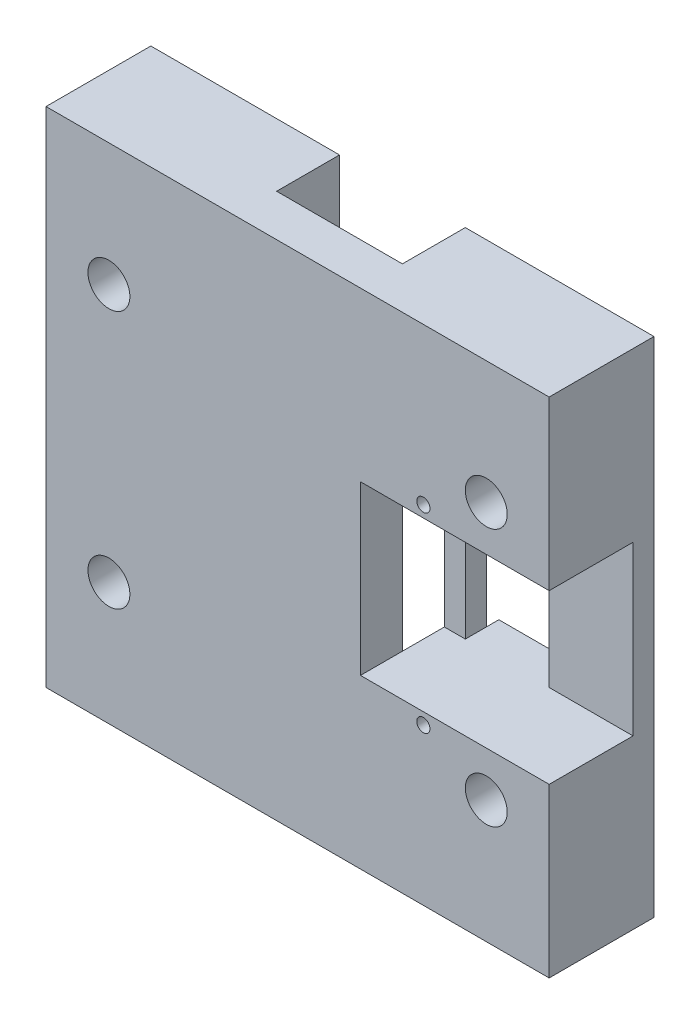
SolidWorks part; units mm, degrees
ref_plane "Front" through (0, 0, 0) normal (0, 0, 1) x (1, 0, 0)
ref_plane "Top" through (0, 0, 0) normal (0, 1, 0) x (1, 0, 0)
ref_plane "Right" through (0, 0, 0) normal (1, 0, 0) x (0, 0, -1)
sketch "Sketch1" plane through (0, 0, 0) normal (0, 0, 1) x (1, 0, 0)
  line L1 (38.1, 10) -> (-38.1, 10) construction
  line L2 (38.1, 10) -> (38.1, -10) construction
  line L3 (38.1, -10) -> (-38.1, -10) construction
  line L4 (-38.1, 10) -> (-38.1, -10) construction
  line L5 (38.1, 10) -> (-38.1, -10) construction
  line L6 (38.1, -10) -> (-38.1, 10) construction
  line L7 (38.1, 38.1) -> (-38.1, 38.1)
  line L8 (38.1, 38.1) -> (38.1, -38.1)
  line L9 (38.1, -38.1) -> (-38.1, -38.1)
  line L10 (-38.1, 38.1) -> (-38.1, -38.1)
  line L11 (38.1, 38.1) -> (-38.1, -38.1) construction
  line L12 (38.1, -38.1) -> (-38.1, 38.1) construction
  circle A0 centre (-28.575, 19.525) radius 3.175
  circle A1 centre (28.575, 19.525) radius 3.175
  circle A2 centre (28.575, -19.525) radius 3.175
  circle A3 centre (-28.575, -19.525) radius 3.175
  point P0 (0, 0)
  point P6 (0, 0)
  point P19 (0, 0)
  point P20 (0, 0)
  point P21 (0, 0)
  point P22 (0, 0)
  point P23 (0, 0)
  point P24 (0, 0)
  point P25 (-28.0713, 19.525)
  point P26 (0, 0)
  point P27 (0, 0)
  point P28 (0, 0)
  point P29 (0, 0)
  point P30 (0, 0)
  point P31 (0, 0)
  point P32 (0, 0)
  point P33 (0, 0)
  point P34 (27.3095, 19.525)
  dimension "D4" = 6.35
  dimension "D1" = 20
  dimension "D2" = 76.2
  dimension "D3" = 76.2
  dimension "D5" = 9.525
  dimension "D6" = 9.525
  dimension "D7" = 9.525
  dimension "D8" = 9.525
extrude "Boss-Extrude1" add sketch "Sketch1" along normal blind 6.35
sketch "Sketch2" plane through (0, 0, 0) normal (0, 0, -1) x (-1, 0, 0)
  line L0 (38.1, -38.1) -> (-38.1, -38.1) construction
  line L1 (9.525, 38.1) -> (-9.525, 38.1)
  line L2 (9.525, 38.1) -> (9.525, -38.1)
  line L3 (9.525, -38.1) -> (-9.525, -38.1)
  line L4 (-9.525, 38.1) -> (-9.525, -38.1)
  line L5 (9.525, 38.1) -> (-9.525, -38.1) construction
  line L6 (9.525, -38.1) -> (-9.525, 38.1) construction
  line L11 (38.1, -38.1) -> (38.1, 38.1)
  line L12 (38.1, 38.1) -> (-38.1, 38.1)
  line L13 (-38.1, 38.1) -> (-38.1, -38.1)
  line L14 (-38.1, -38.1) -> (38.1, -38.1)
  line L15 (38.1, -38.1) -> (38.1, 38.1)
  line L16 (38.1, 38.1) -> (-38.1, 38.1)
  line L17 (-38.1, 38.1) -> (-38.1, -38.1)
  line L18 (-38.1, -38.1) -> (38.1, -38.1)
  point P0 (0, 0)
  circle M6 centre (-28.575, -19.525) radius 3.175
  circle M7 centre (28.575, 19.525) radius 3.175
  line M8 (38.1, -38.1) -> (38.1, 38.1)
  line M9 (38.1, 38.1) -> (-38.1, 38.1)
  line M10 (-38.1, 38.1) -> (-38.1, -38.1)
  line M11 (-38.1, -38.1) -> (38.1, -38.1)
  circle M12 centre (-28.575, 19.525) radius 3.175
  circle M13 centre (28.575, -19.525) radius 3.175
  dimension "D1" = 19.05
  dimension "D2" = 0
extrude "Boss-Extrude3" add sketch "Sketch2" along normal blind 9.525 contours L4 M9 M10 M11 M12 M6 | L2 M9 M11 M8 M13 M7
sketch "Sketch4" plane through (9.525, 0, 0) normal (-1, 0, 0) x (0, 0, 1)
  line L1 (6.35, 12.7) -> (-6.35, 12.7)
  line L2 (6.35, 12.7) -> (6.35, -12.7)
  line L3 (6.35, -12.7) -> (-6.35, -12.7)
  line L4 (-6.35, 12.7) -> (-6.35, -12.7)
  line L5 (6.35, 12.7) -> (-6.35, -12.7) construction
  line L6 (6.35, -12.7) -> (-6.35, 12.7) construction
  line L7 (-9.525, 38.1) -> (-9.525, -38.1) construction
  point P0 (0, 0)
  point P6 (0, 0)
  point P8 (0, 0)
  dimension "D1" = 25.4
  dimension "D2" = 3.175
extrude "Cut-Extrude1" cut sketch "Sketch4" against normal up to surface (28.575 mm away) up to face at (38.1, 0, -1.5875)
sketch "Sketch5" plane through (0, 0, -9.525) normal (0, 0, -1) x (-1, 0, 0)
  line L0 (-28.575, 19.525) -> (-28.575, -19.525) construction
  line L1 (-12.7, 16.2) -> (-25.4, 16.2)
  line L2 (-12.7, 16.2) -> (-12.7, -16.2)
  line L3 (-12.7, -16.2) -> (-25.4, -16.2)
  line L4 (-25.4, 16.2) -> (-25.4, -16.2)
  line L5 (-12.7, 16.2) -> (-25.4, -16.2) construction
  line L6 (-12.7, -16.2) -> (-25.4, 16.2) construction
  line L7 (-9.525, 12.7) -> (-9.525, -12.7) construction
  line L8 (-25.4, 11.2) -> (-25.4, 16.2) construction
  line L9 (-25.4, 16.2) -> (-19.6, 16.2) construction
  point P0 (-19.05, 0)
  point P5 (-30.7455, 0)
  point P6 (0, 0)
  point P7 (0, 0)
  point P13 (-16.1648, 0)
  dimension "D3" = 3.175
extrude "Cut-Extrude2" cut sketch "Sketch5" against normal blind 9.525
sketch "Sketch6" plane through (0, 0, 0) normal (0, 0, -1) x (-1, 0, 0)
  line L0 (-25.4, 16.2) -> (-12.7, 12.7) construction
  line L1 (-25.4, -12.7) -> (-12.7, -16.2) construction
  line L4 (-12.7, 12.7) -> (-12.7, 16.2)
  line L5 (-12.7, 16.2) -> (-25.4, 16.2)
  line L6 (-25.4, 16.2) -> (-25.4, 12.7)
  line L7 (-25.4, 12.7) -> (-12.7, 12.7)
  line L8 (-12.7, 12.7) -> (-12.7, 16.2)
  line L9 (-12.7, 16.2) -> (-25.4, 16.2)
  line L10 (-25.4, 16.2) -> (-25.4, 12.7)
  line L11 (-25.4, 12.7) -> (-12.7, 12.7)
  line L12 (-25.4, -12.7) -> (-25.4, -16.2)
  line L13 (-25.4, -16.2) -> (-12.7, -16.2)
  line L14 (-12.7, -16.2) -> (-12.7, -12.7)
  line L15 (-12.7, -12.7) -> (-25.4, -12.7)
  line L16 (-25.4, -12.7) -> (-25.4, -16.2)
  line L17 (-25.4, -16.2) -> (-12.7, -16.2)
  line L18 (-12.7, -16.2) -> (-12.7, -12.7)
  line L19 (-12.7, -12.7) -> (-25.4, -12.7)
  circle A0 centre (-19.05, 14.45) radius 1
  circle A1 centre (-19.05, -14.45) radius 1
  dimension "D3" = 2
  dimension "D1" = 0
  dimension "D2" = 0
extrude "Cut-Extrude3" cut sketch "Sketch6" against normal up to surface (6.35 mm away) contours A0 | A1 up to face at (11.9063, 0, 6.35)
sketch "Sketch7" plane through (0, 0, 0) normal (0, 0, -1) x (-1, 0, 0)
  line L0 (-25.4, -12.7) -> (-25.4, -16.2) construction
  line L1 (-25.4, -16.2) -> (-12.7, -16.2) construction
  line L2 (-12.7, -16.2) -> (-12.7, -12.7) construction
  line L3 (-12.7, -12.7) -> (-25.4, -12.7) construction
  line L4 (-12.7, 12.7) -> (-12.7, 16.2) construction
  line L5 (-12.7, 16.2) -> (-25.4, 16.2) construction
  line L6 (-25.4, 16.2) -> (-25.4, 12.7) construction
  line L7 (-25.4, 12.7) -> (-12.7, 12.7) construction
  line L8 (-25.4, -12.7) -> (-25.4, -16.2)
  line L9 (-25.4, -16.2) -> (-12.7, -16.2)
  line L10 (-12.7, -16.2) -> (-12.7, -12.7)
  line L11 (-12.7, -12.7) -> (-25.4, -12.7)
  line L12 (-12.7, 12.7) -> (-12.7, 16.2)
  line L13 (-12.7, 16.2) -> (-25.4, 16.2)
  line L14 (-25.4, 16.2) -> (-25.4, 12.7)
  line L15 (-25.4, 12.7) -> (-12.7, 12.7)
  circle A0 centre (-19.05, 14.45) radius 1 construction
  circle A1 centre (-19.05, -14.45) radius 1 construction
  circle A2 centre (-19.05, 14.45) radius 1
  circle A3 centre (-19.05, -14.45) radius 1
extrude "Boss-Extrude4" add sketch "Sketch7" along normal blind 11.43
